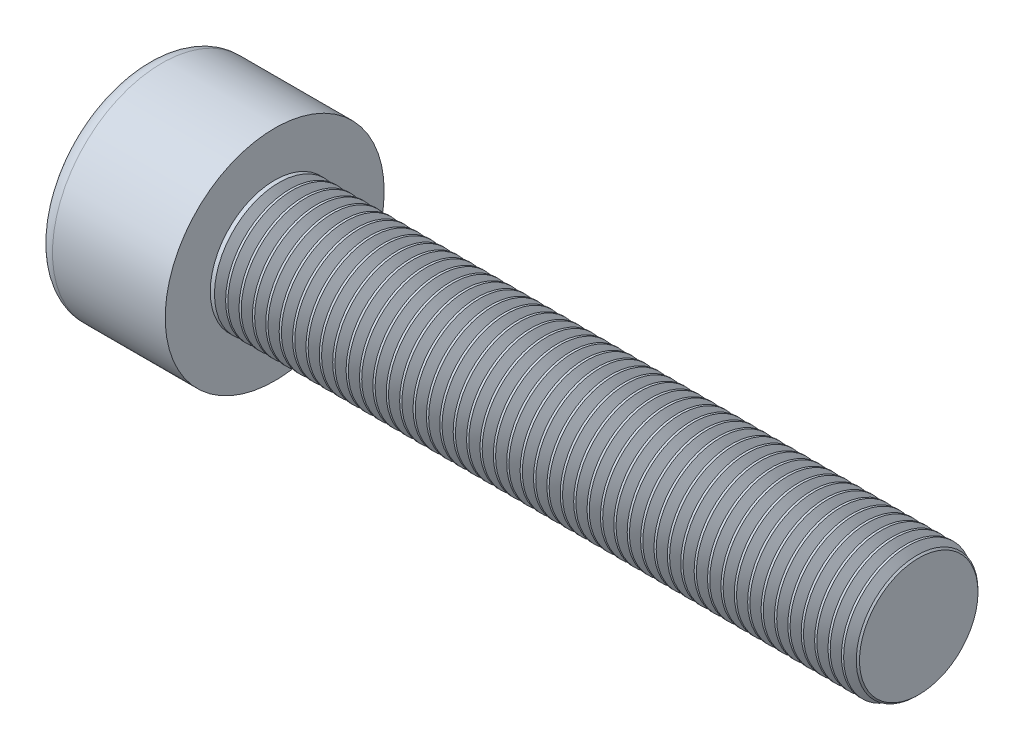
SolidWorks part; units mm, degrees
ref_plane "Front" through (0, 0, 0) normal (0, 0, 1) x (1, 0, 0)
ref_plane "Top" through (0, 0, 0) normal (0, 1, 0) x (1, 0, 0)
ref_plane "Right" through (0, 0, 0) normal (1, 0, 0) x (0, 0, -1)
sketch "Sketch1" plane through (0, 0, 0) normal (1, 0, 0) x (0, 0, -1)
  circle A0 centre (0, 0) radius 4.25
  dimension "dk" = 8.5
extrude "BaseHead" add sketch "Sketch1" along normal blind 5
sketch "Sketch2" plane through (5, 0, 0) normal (1, 0, 0) x (0, 0, -1)
  circle A0 centre (0, 0) radius 2.5
  dimension "d" = 5
extrude "BaseBody" add sketch "Sketch2" along normal blind 25
cosmetic thread "ThreadCosmetic1" [suppressed] parameters "b"=25, "D2"=4.134
sketch "Sketch3" plane through (0, 0, 0) normal (1, 0, 0) x (0, 0, -1)
  line L1 (2.3094, 0) -> (1.1547, 2)
  line L2 (1.1547, 2) -> (-1.1547, 2)
  line L3 (-1.1547, 2) -> (-2.3094, 0)
  line L4 (-2.3094, 0) -> (-1.1547, -2)
  line L5 (-1.1547, -2) -> (1.1547, -2)
  line L6 (1.1547, -2) -> (2.3094, 0)
  circle A0 centre (0, 0) radius 2 construction
  dimension "s" = 4
  dimension "e" = 4.6188
extrude "HexagonSocket" cut sketch "Sketch3" along normal blind 2.5
sketch "Sketch4" plane through (-4.1961, 0.75, 0) normal (0, 0, 1) x (-1, 0, 0)
  line L0 (-6.6961, 2.75) -> (-7.8508, 0.75)
  line L2 (-7.8508, 0.75) -> (-6.6961, 0.75)
  line L3 (-6.6961, 0.75) -> (-6.6961, 2.75)
  line L4 (-5.0351, 0.75) -> (0.839, 0.75) construction
  line L5 (-34.1961, 0.75) -> (-9.1961, 0.75) construction
  line L6 (-9.1961, 0.75) -> (-4.1961, 0.75) construction
  dimension "m" = 60
revolve "Cut-Revolve1" cut sketch "Sketch4" angle 360 about L4
fillet "HeadFillet" [suppressed] radius 0.2
fillet "TopFillet" radius 0.625 1 edges at (0, 0, -4.25)
chamfer "Chamfer1" distance 0.2 angle 45 1 edges at (30, 0, -2.5)
sketch "Sketch5" plane through (0, 0, 0) normal (0, 0, 1) x (1, 0, 0)
  line L0 (29.8, 2.125) -> (30.0165, 2.5)
  line L1 (30.0165, 2.5) -> (30.0165, 2.933)
  line L2 (30.0165, 2.933) -> (29.5835, 2.933)
  line L3 (29.5835, 2.933) -> (29.5835, 2.5)
  line L4 (29.5835, 2.5) -> (29.8, 2.125)
  line L5 (0, 0) -> (7.8886, 0) construction
  line L6 (29.8, -2.5) -> (29.8, 2.5) construction
  dimension "D1" = 5
  dimension "D2" = 0.433
revolve "Cut-Revolve10" cut sketch "Sketch5" angle 360 about L5
pattern_linear "LPattern10" count 48 spacing 0.5196 along (-1, 0, 0) of "Cut-Revolve10"
equation "\"r1@TopFillet\" = \"d@Sketch2\" / 8"
equation "\"D1@Chamfer1\" = \"r@HeadFillet\""
equation "\"D1@Sketch5\" = \"d@Sketch2\""
equation "\"D2@Sketch5\" =  ( \"d@Sketch2\" - \"D2@ThreadCosmetic1\" )  / 2"
equation "\"D3@LPattern10\" = \"D2@Sketch5\" * 1.2"
equation "\"D1@LPattern10\" = \"b@ThreadCosmetic1\" / \"D3@LPattern10\""
